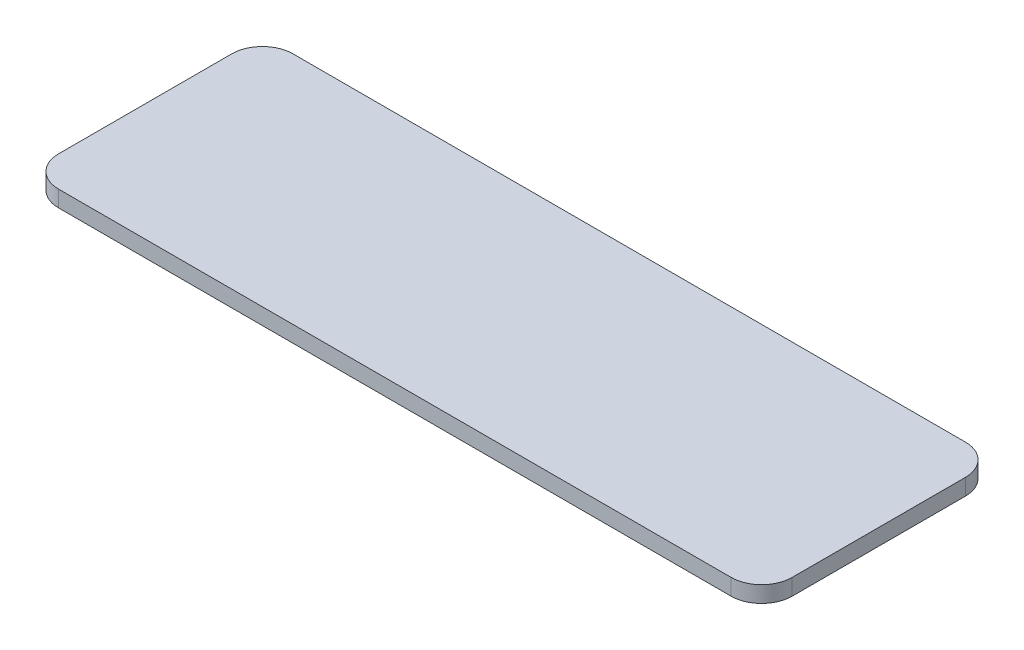
SolidWorks part; units mm, degrees
ref_plane "Front Plane" through (0, 0, 0) normal (0, 0, 1) x (1, 0, 0)
ref_plane "Top Plane" through (0, 0, 0) normal (0, 1, 0) x (1, 0, 0)
ref_plane "Right Plane" through (0, 0, 0) normal (1, 0, 0) x (0, 0, -1)
sketch "Sketch1" plane through (0, 0, 0) normal (0, 1, 0) x (1, 0, 0)
  line L1 (3, 0) -> (69, 0)
  line L2 (0, 3) -> (0, 20)
  line L3 (3, 23) -> (69, 23)
  line L4 (72, 3) -> (72, 20)
  arc A0 (3, 0) -> (0, 3) centre (3, 3) cw
  arc A1 (69, 0) -> (72, 3) centre (69, 3) ccw
  arc A2 (69, 23) -> (72, 20) centre (69, 20) cw
  arc A3 (0, 20) -> (3, 23) centre (3, 20) cw
  point P7 (0, 0)
  point P10 (72, 0)
  point P13 (72, 23)
  dimension "D3" = 3
  dimension "D1" = 72
  dimension "D2" = 23
extrude "Boss-Extrude1" add sketch "Sketch1" along normal blind 1.6
sketch "Sketch2" plane through (0, 1.6, 0) normal (0, 1, 0) x (1, 0, 0)
  line L0 (72, 3) -> (72, 20) construction
  line L1 (69, 23) -> (3, 23) construction
  point P0 (64, 16)
  point P1 (46, 16)
  point P2 (28, 16)
  point P3 (10, 16)
  dimension "D1" = 8
  dimension "D2" = 7
  dimension "D3" = 26
  dimension "D4" = 44
  dimension "D5" = 62
